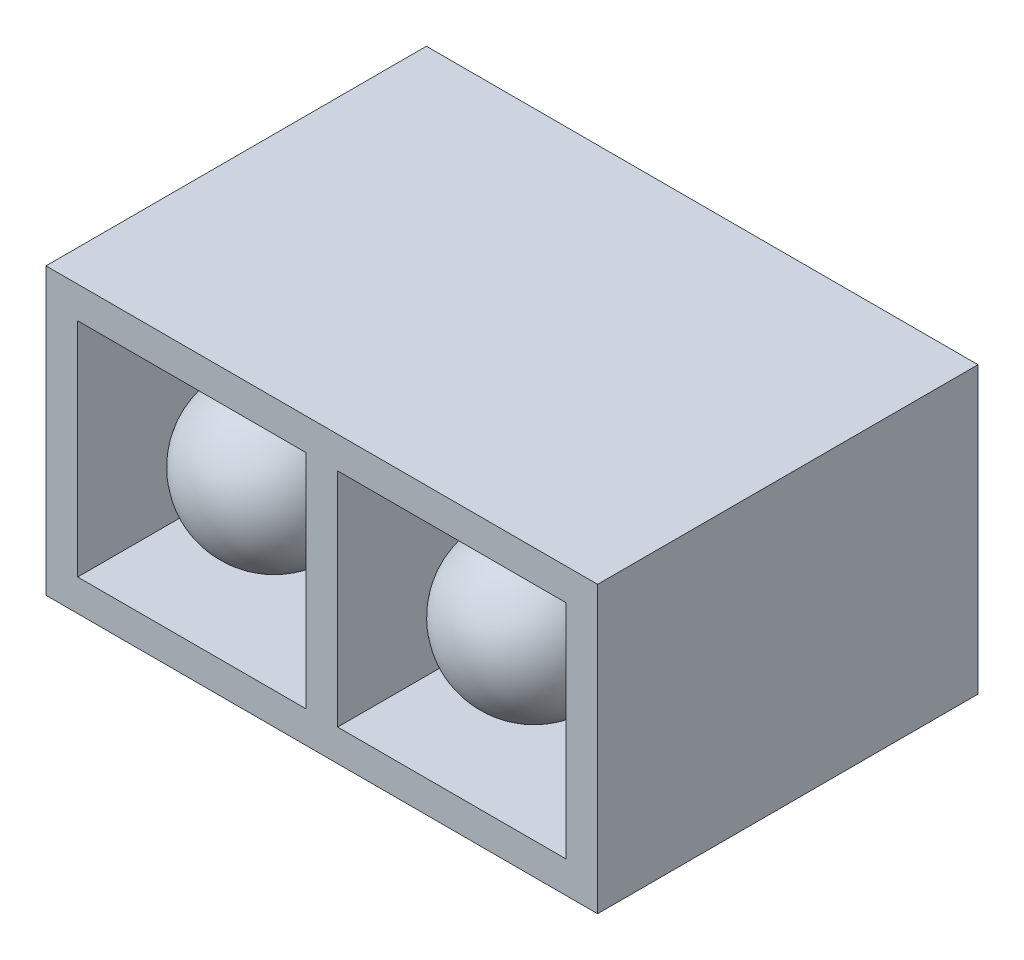
SolidWorks part; units mm, degrees
ref_plane "Plan de face" through (0, 0, 0) normal (0, 0, 1) x (1, 0, 0)
ref_plane "Plan de dessus" through (0, 0, 0) normal (0, 1, 0) x (1, 0, 0)
ref_plane "Plan de droite" through (0, 0, 0) normal (1, 0, 0) x (0, 0, -1)
sketch "Esquisse1" plane through (0, 0, 0) normal (0, 0, 1) x (1, 0, 0)
  line L0 (0, 2.87) -> (0, -2.5096) construction
  line L1 (-4.9678, 0) -> (4.8391, 0) construction
  line L3 (-4.35, 2.25) -> (4.35, 2.25)
  line L4 (-4.35, 2.25) -> (-4.35, -2.25)
  line L5 (-4.35, -2.25) -> (4.35, -2.25)
  line L6 (4.35, 2.25) -> (4.35, -2.25)
  dimension "D1" = 8.7
  dimension "D2" = 4.5
extrude "Extru.-Mince1" add sketch "Esquisse1" along normal blind 6 thin
sketch "Esquisse2" plane through (0, 0, 0) normal (0, 0, 1) x (1, 0, 0)
  line L0 (0, 2.5012) -> (0, -2.5302) construction
  line L2 (4.35, 2.25) -> (-4.35, 2.25) construction
  line L3 (-0.25, 2.25) -> (0.25, 2.25)
  line L4 (-0.25, 2.25) -> (-0.25, -2.25)
  line L5 (-0.25, -2.25) -> (0.25, -2.25)
  line L6 (0.25, 2.25) -> (0.25, -2.25)
  line L7 (-4.35, -2.25) -> (4.35, -2.25) construction
  dimension "D2" = 0.5
extrude "Boss.-Extru.1" add sketch "Esquisse2" along normal blind 6
sketch "Esquisse3" plane through (0, 0, 0) normal (0, 0, -1) x (-1, 0, 0)
  line L1 (-4.35, 2.25) -> (4.35, 2.25)
  line L2 (-4.35, 2.25) -> (-4.35, -2.25)
  line L3 (-4.35, -2.25) -> (4.35, -2.25)
  line L4 (4.35, 2.25) -> (4.35, -2.25)
extrude "Boss.-Extru.2" add sketch "Esquisse3" against normal blind 2
sketch "Esquisse5" plane through (0, 0, 0) normal (0, 1, 0) x (1, 0, 0)
  line L0 (-2.05, -1.1845) -> (-2.05, -6.5255) construction
  line L2 (-0.3863, -4.7) -> (-3.2833, -4.7) construction
  line L4 (-3.25, -4.7) -> (-3.25, -2)
  line L5 (-3.25, -2) -> (-2.05, -2)
  line L7 (4.35, -6) -> (-4.35, -6) construction
  line L8 (-2.05, -2) -> (-2.05, -5.9)
  line L9 (4.35, 0) -> (-4.35, 0) construction
  line L11 (-0.25, -2) -> (-0.25, -6) construction
  line L12 (-3.85, -6) -> (-3.85, -2) construction
  arc A0 (-3.25, -4.7) -> (-2.05, -5.9) centre (-2.05, -4.7) ccw
  dimension "D1" = 2
  dimension "D2" = 1.2
  dimension "D3" = 0.1
revolve "Révolution1" add sketch "Esquisse5" angle 360 about L0
sketch "Esquisse6" plane through (0, 0, 0) normal (0, 1, 0) x (1, 0, 0)
  line L0 (2.05, -1.4061) -> (2.05, -6.3604) construction
  line L1 (0.25, -6) -> (0.25, -2) construction
  line L2 (3.85, -6) -> (3.85, -2) construction
  line L3 (2.05, -4.7) -> (0.469, -4.7) construction
  line L4 (4.35, -6) -> (-4.35, -6) construction
  line L5 (0.85, -4.7) -> (0.85, -2)
  line L6 (0.25, -2) -> (3.85, -2) construction
  line L7 (0.85, -2) -> (2.05, -2)
  line L8 (2.05, -2) -> (2.05, -5.9)
  arc A0 (0.85, -4.7) -> (2.05, -5.9) centre (2.05, -4.7) ccw
  dimension "D1" = 2.4
  dimension "D2" = 0.1
revolve "Révolution2" add sketch "Esquisse6" angle 360 about L0
